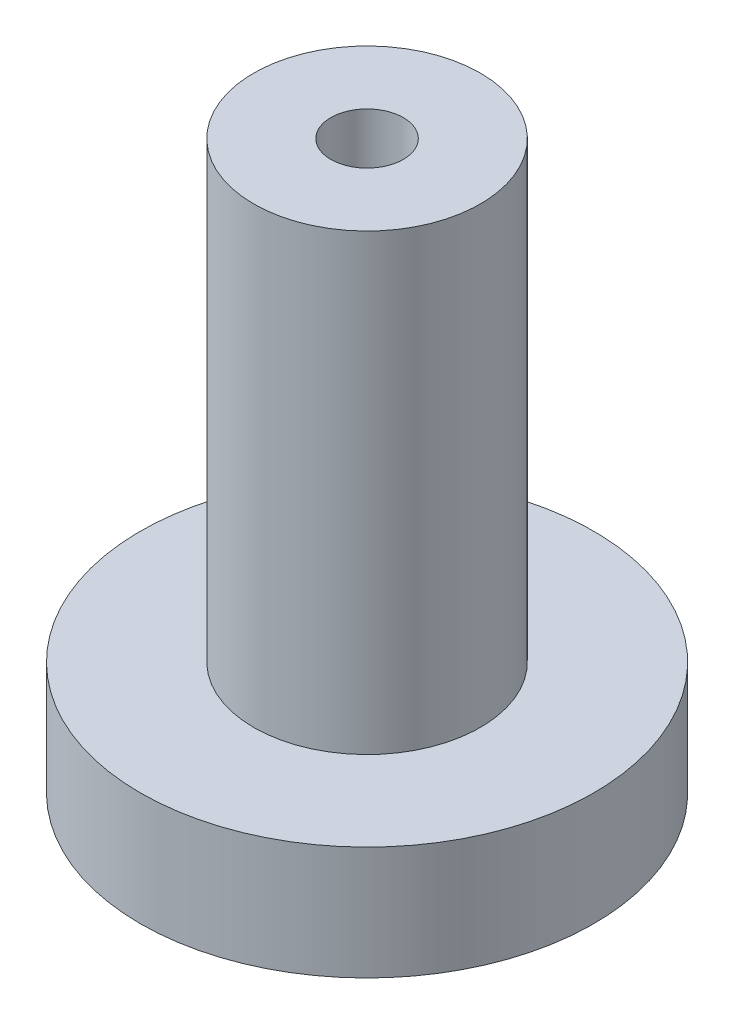
SolidWorks part; units mm, degrees
ref_plane "Front Plane" through (0, 0, 0) normal (0, 0, 1) x (1, 0, 0)
ref_plane "Top Plane" through (0, 0, 0) normal (0, 1, 0) x (1, 0, 0)
ref_plane "Right Plane" through (0, 0, 0) normal (1, 0, 0) x (0, 0, -1)
sketch "Sketch1" plane through (0, 0, 0) normal (0, 1, 0) x (1, 0, 0)
  circle A0 centre (0, 0) radius 12.7
  dimension "D1" = 25.4
extrude "Boss-Extrude1" add sketch "Sketch1" along normal blind 6.35
sketch "Sketch2" plane through (0, 6.35, 0) normal (0, 1, 0) x (1, 0, 0)
  circle A0 centre (0, 0) radius 6.35
  dimension "D1" = 12.7
extrude "Boss-Extrude2" add sketch "Sketch2" along normal blind 25.4
sketch "Sketch3" plane through (0, 31.75, 0) normal (0, 1, 0) x (1, 0, 0)
  circle A0 centre (0, 0) radius 2.032
  dimension "D1" = 4.064
extrude "Cut-Extrude1" cut sketch "Sketch3" against normal blind 5.588
